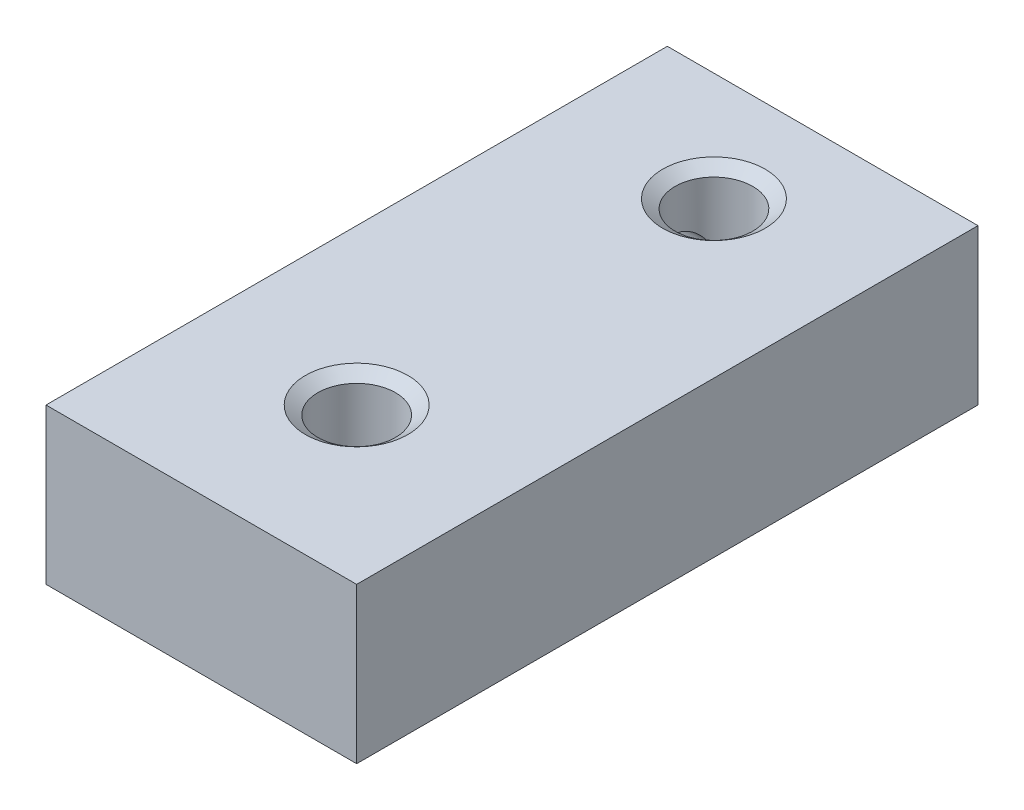
SolidWorks part; units mm, degrees
ref_plane "Спереди" through (0, 0, 0) normal (0, 0, 1) x (1, 0, 0)
ref_plane "Сверху" through (0, 0, 0) normal (0, 1, 0) x (1, 0, 0)
ref_plane "Справа" through (0, 0, 0) normal (1, 0, 0) x (0, 0, -1)
sketch "Эскиз1" plane through (0, 0, 0) normal (0, 0, 1) x (1, 0, 0)
  line L1 (0, 0) -> (10, 0)
  line L2 (0, 0) -> (0, 5)
  line L3 (0, 5) -> (10, 5)
  line L4 (10, 0) -> (10, 5)
  dimension "D1" = 5
  dimension "D2" = 10
extrude "Бобышка-Вытянуть1" add sketch "Эскиз1" along normal blind 20
hole_wizard "Отверстие обработанное метчиком M3x0.51" positions "Эскиз5" profile "Эскиз4" tap size "M3x0.5" standard "Ansi (метрические)" end condition through all
sketch "Эскиз5" plane through (0, 0, 0) normal (0, -1, 0) x (1, 0, 0)
  line L0 (0, 20) -> (10, 20) construction
  line L1 (0, 20) -> (0, 0) construction
  point P0 (5, 15)
  point P1 (5, 3.5)
  dimension "D1" = 5
  dimension "D2" = 11.5
  dimension "D3" = 5
sketch "Эскиз4" plane through (5, 0, 15) normal (1, 0, 0) x (0, 0, -1)
  line L0 (0, 0) -> (0, 5)
  line L1 (0, 5) -> (1.65, 5)
  line L2 (1.25, 4.7199) -> (1.25, 0.2801)
  line L3 (1.25, 0.2801) -> (1.65, 0)
  line L5 (1.65, 0) -> (0, 0)
  line L6 (-1.25, 0.2801) -> (-1.65, 0) construction
  line L7 (1.65, 5) -> (1.25, 4.7199)
  line L8 (-1.65, 5) -> (-1.25, 4.7199) construction
  line L11 (0, -6.35) -> (0, 107.95) construction
  dimension "Диаметр проходного сверла" = 2.5
  dimension "Глубина проходного сверла" = 5
  dimension "Диаметр передней зенковки" = 3.3
  dimension "Угол передней зенковки" = 110
  dimension "Диаметр задней зенковки" = 3.3
  dimension "Угол задней зенковки" = 110
cosmetic thread "Отверстие резьбы3" parameters "D2"=3
cosmetic thread "Отверстие резьбы4" parameters "D2"=3
hole_wizard "Отверстие обработанное метчиком #2-561" positions "Эскиз3" profile "Эскиз2" tap size "#2-56" standard "Ansi (в дюймах)"
sketch "Эскиз3" plane through (0, 0, 0) normal (-1, 0, 0) x (0, 0, 1)
  line L0 (20, 0) -> (0, 0) construction
  line L1 (20, 5) -> (20, 0) construction
  point P0 (3.5, 2.5)
  point P1 (12, 2.5)
  dimension "D1" = 2.5
  dimension "D2" = 8
  dimension "D3" = 8.5
cosmetic thread "Отверстие резьбы1" parameters "D1"=4.5, "D2"=2.1844
cosmetic thread "Отверстие резьбы2" parameters "D1"=4.1213, "D2"=2.1844
sketch "Эскиз2" plane through (0, 2.5, 3.5) normal (0, 1, 0) x (0, 0, 1)
  line L0 (0, 0) -> (0, 6.0342)
  line L1 (0, 6.0342) -> (0.889, 5.5)
  line L2 (0.889, 5.5) -> (0.889, 0.2668)
  line L3 (0.889, 0.2668) -> (1.27, 0)
  line L5 (1.27, 0) -> (0, 0)
  line L6 (-0.889, 0.2668) -> (-1.27, 0) construction
  line L10 (0, 6.0342) -> (-0.889, 5.5) construction
  line L11 (0, -6.35) -> (0, 107.95) construction
  dimension "Диаметр сверла" = 1.778
  dimension "Глубина сверла" = 5.5
  dimension "Диаметр передней зенковки" = 2.54
  dimension "Угол передней зенковки" = 110
  dimension "Угол заточки сверла" = 118
